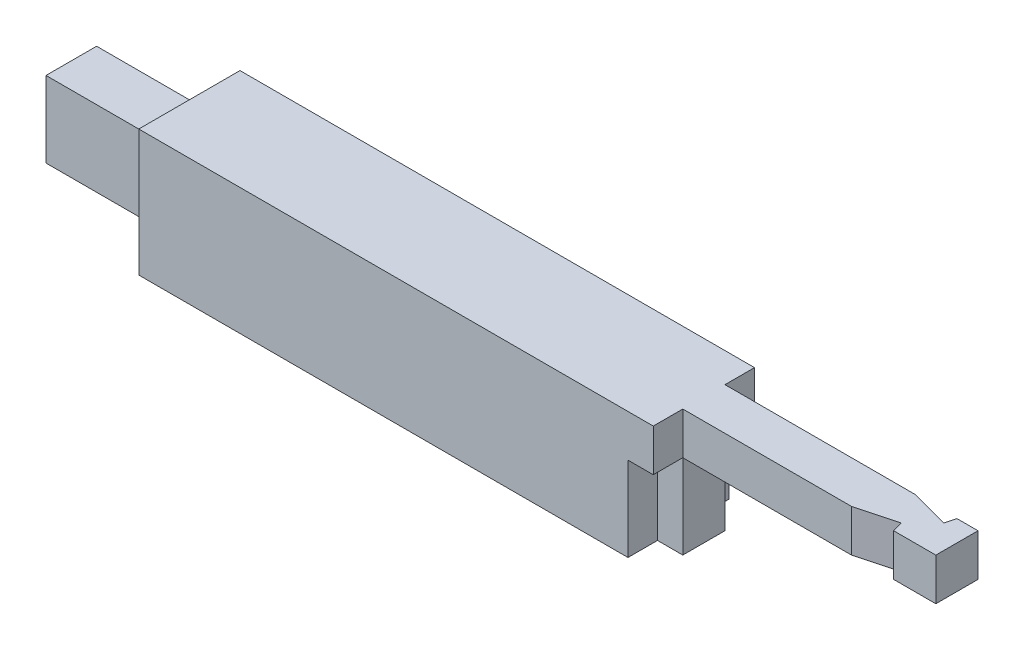
SolidWorks part; units mm, degrees
material "松木"
ref_plane "前视基准面" through (0, 0, 0) normal (0, 0, 1) x (1, 0, 0)
ref_plane "上视基准面" through (0, 0, 0) normal (0, 1, 0) x (1, 0, 0)
ref_plane "右视基准面" through (0, 0, 0) normal (1, 0, 0) x (0, 0, -1)
sketch "草图1" plane through (0, 0, 0) normal (1, 0, 0) x (0, 0, -1)
  line L5 (0, 0) -> (120, 0)
  line L6 (0, 0) -> (0, 150)
  line L7 (0, 150) -> (120, 150)
  line L8 (120, 0) -> (120, 150)
  dimension "D1" = 120
  dimension "D2" = 150
extrude "凸台-拉伸1" add sketch "草图1" along normal blind 610
sketch "草图2" plane through (610, 0, 0) normal (1, 0, 0) x (0, 0, -1)
  line L0 (120, 150) -> (0, 150) construction
  line L1 (35, 150) -> (85, 150)
  line L2 (35, 150) -> (35, 100)
  line L3 (35, 100) -> (85, 100)
  line L4 (85, 150) -> (85, 100)
  line L5 (0, 0) -> (120, 0) construction
  point P6 (60, 100)
  point P9 (60, 0)
  dimension "D1" = 50
  dimension "D2" = 50
extrude "凸台-拉伸2" add sketch "草图2" along normal blind 300
sketch "草图3" plane through (0, 0, 0) normal (-1, 0, 0) x (0, 0, 1)
  line L0 (0, 0) -> (-120, 0) construction
  line L1 (-90, 0) -> (-30, 0)
  line L2 (-90, 0) -> (-90, 150)
  line L3 (-90, 150) -> (-30, 150)
  line L4 (-30, 0) -> (-30, 150)
  line L5 (-120, 150) -> (0, 150) construction
  line L6 (0, 150) -> (0, 0) construction
  line L7 (-90, 120) -> (-30, 120)
  line L8 (-90, 30) -> (-30, 30)
  dimension "D1" = 60
  dimension "D2" = 30
  dimension "D3" = 30
  dimension "D4" = 30
extrude "凸台-拉伸3" add sketch "草图3" along normal blind 140 contours L2 L8 L4 L7
sketch "草图4" plane through (610, 0, 0) normal (1, 0, 0) x (0, 0, -1)
  line L1 (35, 100) -> (0, 100)
  line L2 (35, 100) -> (35, 0)
  line L3 (35, 0) -> (0, 0)
  line L4 (0, 100) -> (0, 0)
  line L5 (85, 100) -> (120, 100)
  line L6 (85, 100) -> (85, 0)
  line L7 (85, 0) -> (120, 0)
  line L8 (120, 100) -> (120, 0)
extrude "切除-拉伸1" cut sketch "草图4" against normal blind 30
sketch "草图5" plane through (0, 150, 0) normal (0, 1, 0) x (1, 0, 0)
  line L0 (910, 35) -> (860, 35)
  line L1 (910, 35) -> (610, 35) construction
  line L2 (860, 35) -> (860, 48.3975)
  line L3 (860, 48.3975) -> (810, 35)
  line L4 (860, 35) -> (856.6506, 47.5)
  line L5 (910, 85) -> (885, 85)
  line L6 (910, 85) -> (610, 85) construction
  line L7 (885, 85) -> (881.6506, 72.5)
  line L8 (881.6506, 72.5) -> (835, 85)
  line L9 (810, 35) -> (860, 35)
  line L10 (835, 85) -> (885, 85)
  line M11 (610, 35) -> (910, 35)
  line M13 (910, 85) -> (610, 85)
  dimension "D1" = 50
  dimension "D2" = 50
  dimension "D3" = 15
  dimension "D4" = 15
  dimension "D5" = 50
  dimension "D6" = 25
  dimension "D7" = 75
  dimension "D8" = 15
extrude "切除-拉伸2" cut sketch "草图5" against normal through all contours L4 L3 M11 | L8 L7 M13
